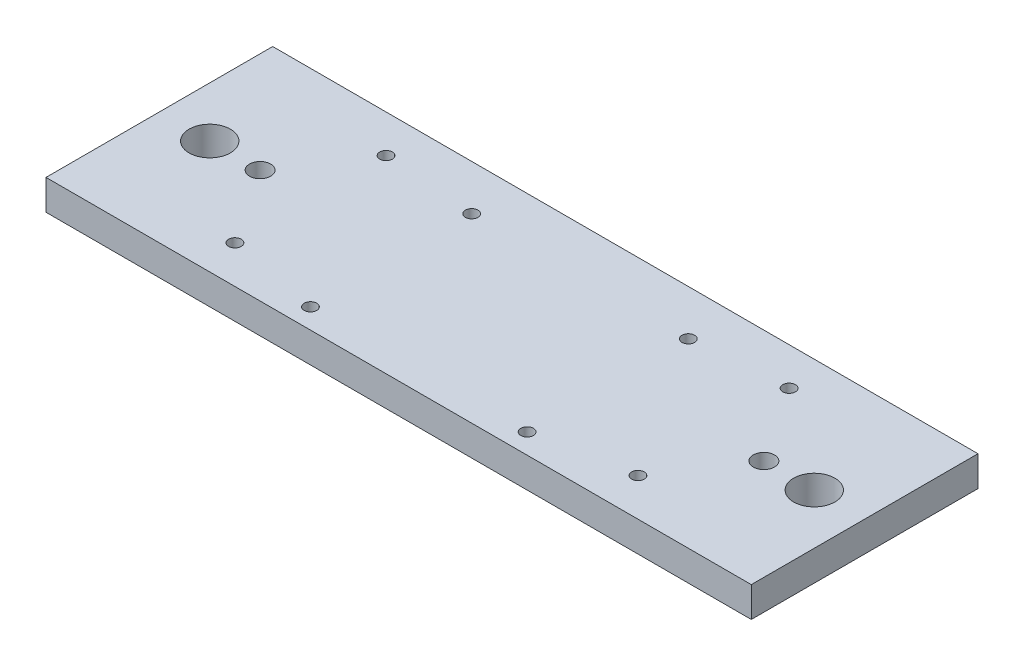
SolidWorks part; units mm, degrees
material "PVC"
ref_plane "前视基准面" through (0, 0, 0) normal (0, 0, 1) x (1, 0, 0)
ref_plane "上视基准面" through (0, 0, 0) normal (0, 1, 0) x (1, 0, 0)
ref_plane "右视基准面" through (0, 0, 0) normal (1, 0, 0) x (0, 0, -1)
sketch "草图1" plane through (0, 0, 0) normal (0, 1, 0) x (1, 0, 0)
  line L0 (0, 0) -> (0, 53.9417) construction
  line L1 (-70, 22.5) -> (70, 22.5)
  line L2 (-70, 22.5) -> (-70, -22.5)
  line L3 (-70, -22.5) -> (70, -22.5)
  line L4 (70, 22.5) -> (70, -22.5)
  line L5 (0, 0) -> (96.6368, 0) construction
  circle A0 centre (60, 0) radius 4.1
  circle A1 centre (-60, 0) radius 4.1
  circle A2 centre (-40, 15) radius 0.5
  circle A3 centre (40, 15) radius 0.5
  circle A4 centre (40, -15) radius 0.5
  circle A5 centre (-40, -15) radius 0.5
  dimension "D1" = 80
  dimension "D2" = 30
  dimension "D5" = 120
  dimension "D6" = 8.2
  dimension "D7" = 1
  dimension "D3" = 45
  dimension "D4" = 140
extrude "凸台-拉伸1" add sketch "草图1" along normal blind 6
hole_wizard "M3 Tapped Hole5" positions "草图3" profile "草图2" tap size "M3" standard "GB" end condition through all
sketch "草图3" plane through (0, 6, 0) normal (0, 1, 0) x (1, 0, 0)
  point P0 (-40, 15)
  point P3 (-40, -15)
  point P6 (40, -15)
  point P9 (40, 15)
cosmetic thread "Hole Thread9" parameters "D2"=3
cosmetic thread "Hole Thread10" parameters "D2"=3
cosmetic thread "Hole Thread11" parameters "D2"=3
cosmetic thread "Hole Thread12" parameters "D2"=3
sketch "草图2" plane through (-40, 6, -15) normal (1, 0, 0) x (0, 0, 1)
  line L0 (0, 0) -> (0, 6)
  line L1 (0, 6) -> (1.25, 6)
  line L2 (1.25, 6) -> (1.25, 0)
  line L5 (1.25, 0) -> (0, 0)
  line L11 (0, -6.35) -> (0, 107.95) construction
  dimension "Thru Tap Drill Dia." = 2.5
  dimension "Thru Tap Drill Depth" = 6
sketch "Sketch2" plane through (0, 6, 0) normal (0, 1, 0) x (1, 0, 0)
  line L0 (70, 22.5) -> (-70, 22.5) construction
  line L1 (-21.5, -18.5) -> (21.5, -18.5)
  line L2 (-21.5, -18.5) -> (-21.5, 13.5)
  line L3 (-21.5, 13.5) -> (21.5, 13.5)
  line L4 (21.5, -18.5) -> (21.5, 13.5)
  line L5 (-21.5, -18.5) -> (21.5, 13.5) construction
  line L6 (-21.5, 13.5) -> (21.5, -18.5) construction
  point P0 (0, -2.5)
  dimension "D1" = 43
  dimension "D2" = 32
  dimension "D3" = 25
hole_wizard "M3 Tapped Hole2" positions "Sketch4" profile "Sketch3" tap size "M3" standard "GB" end condition through all
sketch "Sketch4" plane through (0, 6, 0) normal (0, 1, 0) x (1, 0, 0)
  point P0 (-21.5, 13.5)
  point P3 (21.5, 13.5)
  point P6 (21.5, -18.5)
  point P9 (-21.5, -18.5)
sketch "Sketch3" plane through (-21.5, 6, -13.5) normal (1, 0, 0) x (0, 0, 1)
  line L0 (0, 0) -> (0, 6)
  line L1 (0, 6) -> (1.25, 6)
  line L2 (1.25, 6) -> (1.25, 0)
  line L5 (1.25, 0) -> (0, 0)
  line L11 (0, -6.35) -> (0, 107.95) construction
  dimension "Thru Tap Drill Dia." = 2.5
  dimension "Thru Tap Drill Depth" = 6
cosmetic thread "Hole Thread5" parameters "D2"=3
cosmetic thread "Hole Thread6" parameters "D2"=3
cosmetic thread "Hole Thread7" parameters "D2"=3
cosmetic thread "Hole Thread8" parameters "D2"=3
hole_wizard "Ø4.2 (4.2) 直径孔1" positions "草图5" profile "草图4" hole size "Ø4.2" standard "GB" end condition through all
sketch "草图5" plane through (0, 6, 0) normal (0, 1, 0) x (1, 0, 0)
  point P0 (50, 0)
  point P2 (-50, 0)
  dimension "D1" = 100
  dimension "D2" = 50
sketch "草图4" plane through (50, 6, 0) normal (1, 0, 0) x (0, 0, 1)
  line L0 (0, 0) -> (0, 6)
  line L1 (0, 6) -> (2.1, 6)
  line L2 (2.1, 6) -> (2.1, 0)
  line L5 (2.1, 0) -> (0, 0)
  line L11 (0, -6.35) -> (0, 107.95) construction
  dimension "通孔孔直径" = 4.2
  dimension "通孔孔深度" = 6
